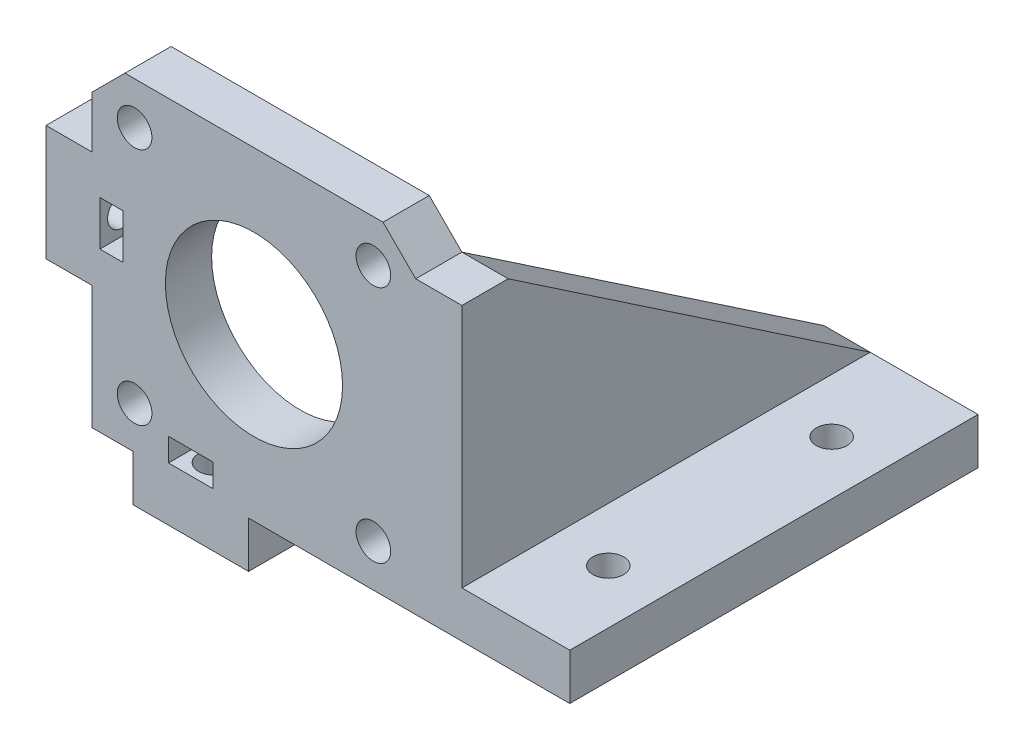
SolidWorks part; units mm, degrees
ref_plane "Plan de face" through (0, 0, 0) normal (0, 0, 1) x (1, 0, 0)
ref_plane "Plan de dessus" through (0, 0, 0) normal (0, 1, 0) x (1, 0, 0)
ref_plane "Plan de droite" through (0, 0, 0) normal (1, 0, 0) x (0, 0, -1)
other "plexi"
sketch "Esquisse1" plane through (0, 0, 0) normal (0, 0, 1) x (1, 0, 0)
  line L0 (0, 0) -> (0, 16)
  line L1 (0, 0) -> (5.3, 0)
  line L2 (0, 31) -> (0, 37.7574)
  line L3 (0, 37.7574) -> (4.2426, 42)
  line L4 (4.2426, 42) -> (37.7574, 42)
  line L5 (37.7574, 42) -> (42, 37.7574)
  line L6 (42, 37.7574) -> (42, 0)
  line L7 (42, 0) -> (20.3, 0)
  line L8 (0, 31) -> (-6, 31)
  line L9 (-6, 31) -> (-6, 16)
  line L10 (-6, 16) -> (0, 16)
  line L11 (5.3, 0) -> (5.3, -6)
  line L12 (5.3, -6) -> (20.3, -6)
  line L13 (20.3, -6) -> (20.3, 0)
  line L14 (-6, 23.5) -> (9.0323, 23.5) construction
  line L15 (12.8, -6) -> (12.8, 12.9371) construction
  line L16 (1, 20.6) -> (4, 20.6)
  line L17 (1, 20.6) -> (1, 26.4)
  line L18 (1, 26.4) -> (4, 26.4)
  line L19 (4, 20.6) -> (4, 26.4)
  line L20 (1, 20.6) -> (4, 26.4) construction
  line L21 (1, 26.4) -> (4, 20.6) construction
  line L22 (21, 21) -> (36.5, 21) construction
  line L23 (9.9, 4) -> (15.7, 4)
  line L24 (9.9, 4) -> (9.9, 1)
  line L25 (9.9, 1) -> (15.7, 1)
  line L26 (15.7, 4) -> (15.7, 1)
  line L27 (9.9, 4) -> (15.7, 1) construction
  line L28 (9.9, 1) -> (15.7, 4) construction
  line L29 (5.5, 36.5) -> (36.5, 36.5) construction
  line L30 (5.5, 36.5) -> (5.5, 5.5) construction
  line L31 (5.5, 5.5) -> (36.5, 5.5) construction
  line L32 (36.5, 36.5) -> (36.5, 5.5) construction
  line L33 (21, 21) -> (21, 5.5) construction
  circle A0 centre (21, 21) radius 11.5
  circle A1 centre (5.5, 36.5) radius 2.25
  circle A2 centre (36.5, 36.5) radius 2.25
  circle A3 centre (5.5, 5.5) radius 2.25
  circle A4 centre (36.5, 5.5) radius 2.25
  point P27 (2.5, 23.5)
  point P34 (12.8, 2.5)
  dimension "D4" = 23
  dimension "D5" = 42
  dimension "D10" = 4.5
  dimension "D1" = 16
  dimension "D2" = 5.3
  dimension "D3" = 42
  dimension "D6" = 21
  dimension "D7" = 21
  dimension "D8" = 6
  dimension "D9" = 135
  dimension "D13" = 31
  dimension "D15" = 6
  dimension "D23" = 15
  dimension "D24" = 6
  dimension "D25" = 15
  dimension "D26" = 7
  dimension "D27" = 5.8
  dimension "D28" = 3
  dimension "D31" = 7
extrude "Boss.-Extru.2" add sketch "Esquisse1" along normal blind 6
sketch "Esquisse9" plane through (42, 0, 0) normal (1, 0, 0) x (0, 0, -1)
  line L0 (-6, 0) -> (47, 0)
  line L1 (47, 0) -> (47, 6)
  line L2 (47, 6) -> (0, 37.7574)
  line L3 (0, 37.7574) -> (-6, 37.7574)
  line L4 (-6, 37.7574) -> (-6, 0)
  dimension "D1" = 53
  dimension "D2" = 6
extrude "Boss.-Extru.4" add sketch "Esquisse9" along normal blind 6
sketch "Esquisse11" plane through (0, 0, 0) normal (0, -1, 0) x (1, 0, 0)
  line L0 (55, -47) -> (55, 6) construction
  line L1 (48, -47) -> (62, -47)
  line L2 (48, -47) -> (48, 6)
  line L3 (48, 6) -> (62, 6)
  line L4 (62, -47) -> (62, 6)
  circle A0 centre (55, -35) radius 2
  circle A1 centre (55, -6) radius 2
  dimension "D6" = 4
  dimension "D1" = 14
  dimension "D3" = 12
  dimension "D4" = 53
  dimension "D5" = 12
extrude "Boss.-Extru.5" add sketch "Esquisse11" against normal blind 6
sketch "Esquisse13" plane through (-6, 0, 0) normal (-1, 0, 0) x (0, 0, 1)
  line L0 (3, 31) -> (3, 16) construction
  line L1 (6, 31) -> (0, 31) construction
  line L2 (6, 16) -> (0, 16) construction
  line L3 (6, 23.5) -> (0, 23.5) construction
  line L4 (6, 31) -> (6, 16) construction
  line L5 (0, 31) -> (0, 16) construction
  circle A0 centre (3, 23.5) radius 2
  dimension "D1" = 4
extrude "Enlèv. mat.-Extru.1" cut sketch "Esquisse13" against normal blind 14
sketch "Esquisse14" plane through (0, -6, 0) normal (0, -1, 0) x (1, 0, 0)
  line L0 (5.3, 3) -> (20.3, 3) construction
  line L1 (5.3, 6) -> (5.3, 0) construction
  line L2 (20.3, 6) -> (20.3, 0) construction
  line L3 (12.8, 6) -> (12.8, 0) construction
  line L4 (5.3, 6) -> (20.3, 6) construction
  line L5 (5.3, 0) -> (20.3, 0) construction
  circle A0 centre (12.8, 3) radius 2
  dimension "D1" = 4
extrude "Enlèv. mat.-Extru.2" cut sketch "Esquisse14" against normal blind 14
